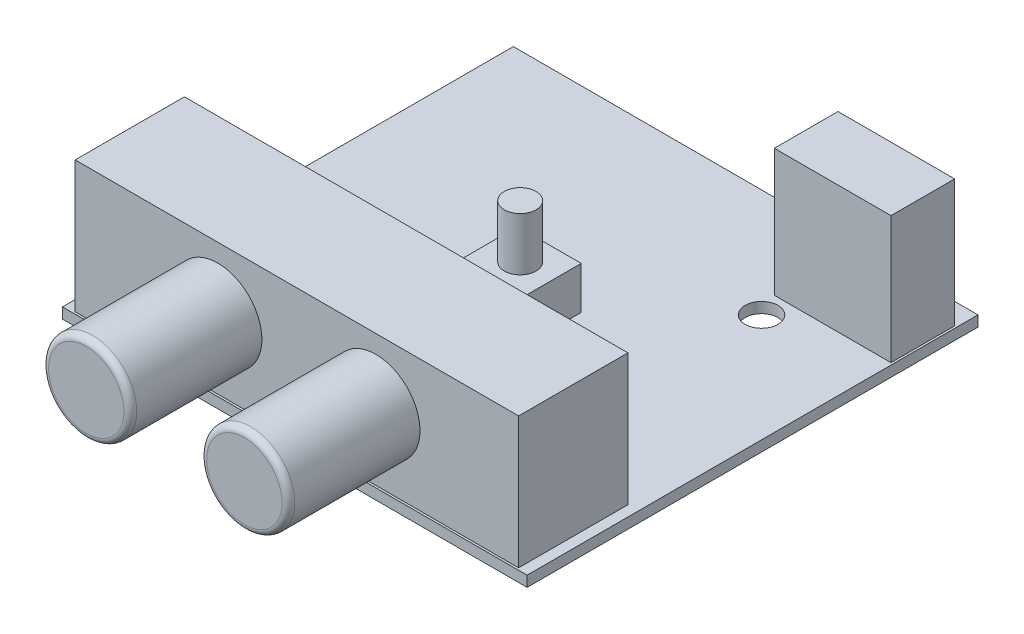
SolidWorks part; units mm, degrees
ref_plane "Front Plane" through (0, 0, 0) normal (0, 0, 1) x (1, 0, 0)
ref_plane "Top Plane" through (0, 0, 0) normal (0, 1, 0) x (1, 0, 0)
ref_plane "Right Plane" through (0, 0, 0) normal (1, 0, 0) x (0, 0, -1)
sketch "Sketch1" plane through (0, 0, 0) normal (0, 1, 0) x (1, 0, 0)
  line L1 (21.9, -21.25) -> (-21.9, -21.25)
  line L2 (21.9, -21.25) -> (21.9, 21.25)
  line L3 (21.9, 21.25) -> (-21.9, 21.25)
  line L4 (-21.9, -21.25) -> (-21.9, 21.25)
  line L5 (21.9, -21.25) -> (-21.9, 21.25) construction
  line L6 (21.9, 21.25) -> (-21.9, -21.25) construction
  point P0 (0, 0)
  dimension "D1" = 43.8
  dimension "D2" = 42.5
extrude "Boss-Extrude1" add sketch "Sketch1" along normal blind 1
sketch "Sketch2" plane through (0, 1, 0) normal (0, 1, 0) x (1, 0, 0)
  line L1 (-20.9, -10.75) -> (20.9, -10.75)
  line L2 (-20.9, -10.75) -> (-20.9, -21.05)
  line L3 (-20.9, -21.05) -> (20.9, -21.05)
  line L4 (20.9, -10.75) -> (20.9, -21.05)
  line L6 (0, -10.75) -> (0, 0) construction
  line L7 (21.9, -21.25) -> (21.9, 21.25) construction
  line L8 (-21.9, -21.25) -> (21.9, -21.25) construction
  point P7 (20.9, -20.4095)
  point P11 (0, 0)
  dimension "D1" = 10.3
  dimension "D2" = 1
  dimension "D3" = 0.2
extrude "Boss-Extrude2" add sketch "Sketch2" along normal blind 12.4
sketch "Sketch3" plane through (0, 0, 21.05) normal (0, 0, 1) x (1, 0, 0)
  line L0 (-7.45, 7.55) -> (7.45, 7.55) construction
  line L1 (0, 0) -> (0, 7.55) construction
  line L2 (-21.9, 0) -> (21.9, 0) construction
  circle A0 centre (7.45, 7.55) radius 4.15
  circle A1 centre (-7.45, 7.55) radius 4.15
  point P8 (-11.6, 7.55)
  point P9 (11.6, 7.55)
  point P10 (7.45, 11.7)
  dimension "D1" = 8.3
  dimension "D2" = 23.2
  dimension "D3" = 11.7
extrude "Boss-Extrude3" add sketch "Sketch3" along normal blind 12.4
sketch "Sketch4" plane through (0, 1, 0) normal (0, 1, 0) x (1, 0, 0)
  line L0 (21.9, -21.25) -> (21.9, 21.25) construction
  line L1 (10.7, 13.25) -> (21.7, 13.25)
  line L2 (10.7, 13.25) -> (10.7, 19.25)
  line L3 (10.7, 19.25) -> (21.7, 19.25)
  line L4 (21.7, 13.25) -> (21.7, 19.25)
  line L5 (21.9, 21.25) -> (-21.9, 21.25) construction
  point P4 (19.1244, 14.1783)
  dimension "D1" = 6
  dimension "D2" = 11
  dimension "D3" = 0.2
  dimension "D4" = 2
extrude "Boss-Extrude4" add sketch "Sketch4" along normal blind 12
sketch "Sketch5" plane through (0, 1, 0) normal (0, 1, 0) x (1, 0, 0)
  line L0 (0, 0) -> (0, -3.25) construction
  line L1 (-3, 2.75) -> (3, 2.75)
  line L2 (-3, 2.75) -> (-3, -3.25)
  line L3 (-3, -3.25) -> (3, -3.25)
  line L4 (3, 2.75) -> (3, -3.25)
  line L5 (21.9, 21.25) -> (-21.9, 21.25) construction
  dimension "D1" = 6
  dimension "D2" = 18.5
extrude "Boss-Extrude5" add sketch "Sketch5" along normal blind 4
sketch "Sketch6" plane through (0, 5, 0) normal (0, 1, 0) x (1, 0, 0)
  circle A0 centre (0, 0) radius 1.5
  dimension "D1" = 3
extrude "Boss-Extrude6" add sketch "Sketch6" along normal offset from surface (5 mm away) 9 up to face at (0, 1, 0) offset beyond the face yes
sketch "Sketch7" plane through (0, 1, 0) normal (0, 1, 0) x (1, 0, 0)
  line L0 (21.9, -21.25) -> (21.9, 21.25) construction
  line L1 (21.9, 21.25) -> (-21.9, 21.25) construction
  circle A0 centre (11.7, 11.05) radius 1.55
  point P2 (0, 0)
  dimension "D1" = 3.1
  dimension "D2" = 10.2
  dimension "D3" = 10.2
extrude "Cut-Extrude1" cut sketch "Sketch7" against normal through all
fillet "Fillet1" radius 0.6 2 edges at (11.6, 7.55, 33.45) (-3.3, 7.55, 33.45)
